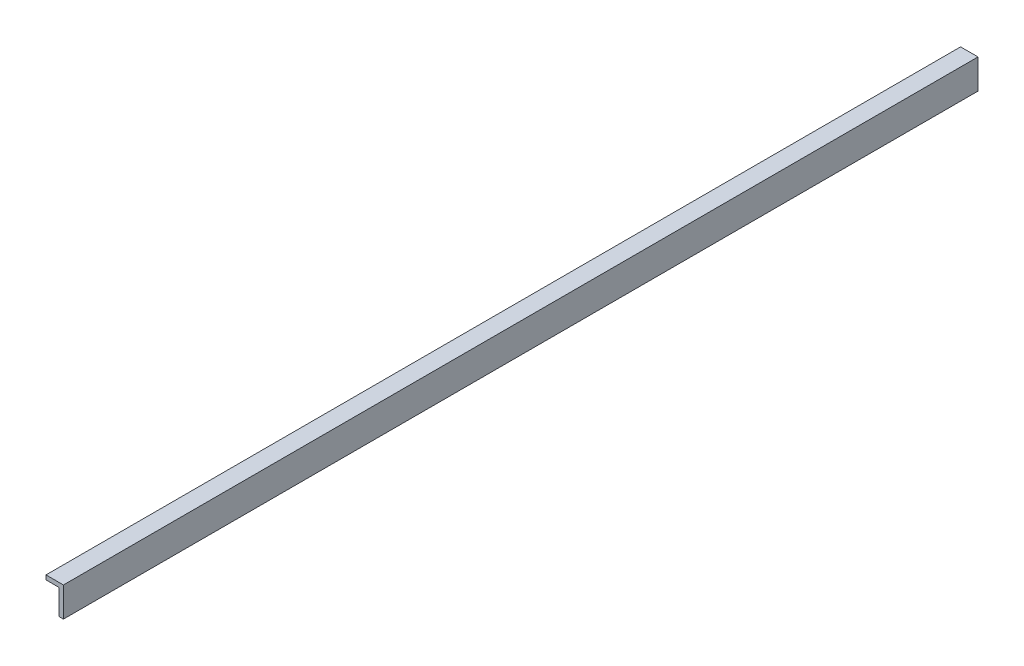
SolidWorks part; units mm, degrees
material "ABS"
ref_plane "Alzado" through (0, 0, 0) normal (0, 0, 1) x (1, 0, 0)
ref_plane "Planta" through (0, 0, 0) normal (0, 1, 0) x (1, 0, 0)
ref_plane "Vista lateral" through (0, 0, 0) normal (1, 0, 0) x (0, 0, -1)
sketch "Croquis1" plane through (0, 0, 0) normal (0, 0, 1) x (1, 0, 0)
  line L1 (0, 0) -> (-5, 0)
  line L2 (0, 0) -> (0, 34)
  line L3 (0, 34) -> (-5, 34)
  line L4 (-5, 0) -> (-5, 34)
  line L5 (-5, 34) -> (-20, 34)
  line L6 (-5, 34) -> (-5, 29)
  line L7 (-5, 29) -> (-20, 29)
  line L8 (-20, 34) -> (-20, 29)
  dimension "D1" = 34
  dimension "D2" = 5
  dimension "D3" = 15
  dimension "D4" = 5
extrude "Saliente-Extruir1" add sketch "Croquis1" against normal blind 1050 contours L5 L8 L7 L6 | L4 L1 L2 L3
